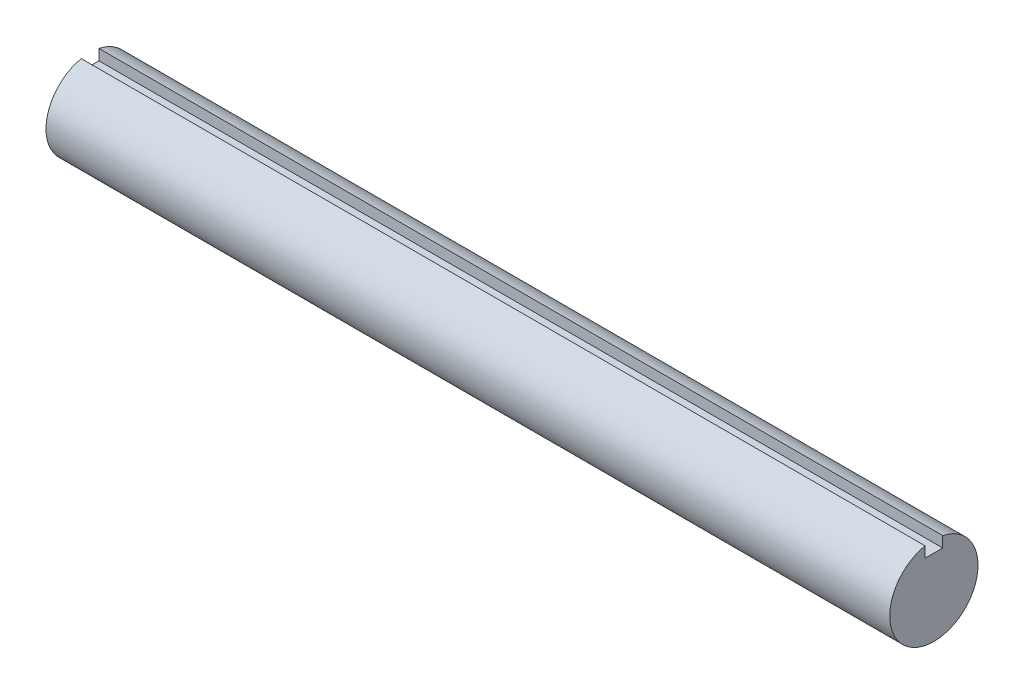
SolidWorks part; units mm, degrees
ref_plane "Front" through (0, 0, 0) normal (0, 0, 1) x (1, 0, 0)
ref_plane "Top" through (0, 0, 0) normal (0, 1, 0) x (1, 0, 0)
ref_plane "Right" through (0, 0, 0) normal (1, 0, 0) x (0, 0, -1)
sketch "AxleProfile" plane through (0, 0, 0) normal (1, 0, 0) x (0, 0, -1)
  line L0 (0, 0) -> (0, 4.8852) construction
  line L1 (-1.331, 6.5042) -> (-1.331, 4.8852)
  line L2 (-1.331, 4.8852) -> (1.331, 4.8852)
  line L3 (1.331, 4.8852) -> (1.331, 6.5042)
  arc A0 (-1.331, 6.5042) -> (1.331, 6.5042) centre (0, 0) ccw
  dimension "D1" = 13.278
  dimension "D2" = 2.662
  dimension "D3" = 1.619
  dimension "D4" = 1.619
extrude "AxleExtrude" add sketch "AxleProfile" along normal blind 127
equation "\"CageLeftBottomEdge\"=22.11mm"
equation "\"CageLeftTopEdge\"=22.11mm"
equation "\"CageRightBottomEdge\"=21.63mm"
equation "\"CageRightTopEdge\"=21.63mm"
equation "\"CageHeight\"=86.04mm"
equation "\"CageLength\"=73.76mm"
equation "\"CageTopScrewClearance\"=10mm"
equation "\"CageBottomScrewClearance\"=25mm"
equation "\"CageLeftTopDepth\"= 11.65mm"
equation "\"CageLeftBottomDepth\"=11.11mm"
equation "\"CageLeftTopHeight\"=8.56175mm"
equation "\"CageLeftBottomHeight\"=16mm"
equation "\"CageRightTopDepth\"= 11.05mm"
equation "\"CageRightBottomDepth\"=10.58mm"
equation "\"CageRightTopHeight\"=9.6mm"
equation "\"CageRightBottomHeight\"=15.49mm"
equation "\"CageLeftTopChannelDepth\"=2.41908mm"
equation "\"CageLeftBottomChannelDepth\"=2.588mm"
equation "\"CageLeftChannelHeight\"=11.7mm"
equation "\"CageRightTopChannelDepth\"=2.32mm"
equation "\"CageRightBottomChannelDepth\"=2.318mm"
equation "\"CageRightChannelHeight\"=10mm"
equation "\"CageChanRelHeight\"=23.99mm"
equation "\"CageChanRelDepth\"=5.492mm"
equation "\"CageChamberRadius\"=16.261mm"
equation "\"CageScrewDiameter\"=4.8mm"
equation "\"CageSetScrewDiameter\"=3.5mm"
equation "\"CageAxleRadius\"=6.639mm"
equation "\"CageAxleKeyHeight\"=1.619mm"
equation "\"CageAxleKeyWidth\"=2.662mm"
equation "\"CageHoseWindowWidth\"=16.29mm"
equation "\"CageHoseWindowHeight\"=26.5mm"
equation "\"CageHoseWindow-Edge\"=8.89mm"
equation "\"CageScrew-VerticalEdge\"=5.0mm"
equation "\"CageScrew-HorizontalEdge\"=7.5mm"
equation "\"CageScrew-HoseCornerScrewEdge\"=4.45mm"
equation "\"CageAxle-BottomEdge\"=56.05mm"
equation "\"CageAxle-FrontEdge\"=46.03mm"
equation "\"CageBackSetScrew-Axle\"=40mm"
equation "\"CageFrontSetScrew-Axle\"=22mm"
equation "\"CageVelocityWindow-BackEdge\"=34.8mm"
equation "\"CageVelocityWindow-BottomEdge\"=27.55mm"
equation "\"CageVelocityWindowHeight\"=22.29mm"
equation "\"CageVelocityWindowWidth\"=12.61mm"
equation "\"TriggerSlot-BottomEdge\"=6.35mm"
equation "\"TriggerSlot-FrontEdge\"=15mm"
equation "\"TriggerSlotSize\"=6.7mm"
equation "\"TriggerRackOffset\"=6mm"
equation "\"TriggerSlotSizeInt\"=.25in"
equation "\"MotorMountLegLength\"=.25in"
equation "\"GearOffset\"=.264907in"
equation "\"TriggerSlotSpacing\"=.25in"
equation "\"TriggerMiniSlotWidth\"=3.5mm"
equation "\"TriggerRackWidth\"=6.5mm"
equation "\"gearhubintdiam\"=30mm"
equation "\"gearhubintwid\"=12.21mm"
equation "\"vigorwidth\"= 0.472441in"
equation "\"vigorflangewidth\"= 0.731102in"
equation "\"vigorflangelength\"= 0.131102in"
equation "\"vigorscrewsize\"= 0.066535in"
equation "\"vigorholeoffsetwid\"= 0.0646653in"
equation "\"vigorholeoffsetlen\"= 0.065551in"
equation "\"vigorflangedepth\"= 0.0901575in"
equation "\"vigordiscdepth\"= 0.0492126in"
equation "\"vigormotordepth\"= 1.12362in"
equation "\"vigortipdepth\"= 0.259055in"
equation "\"vigoraxlewidth\"= 0.173622in"
equation "\"vigorcutlen\"= 0.0480315in"
equation "\"vigoraxledepth\"= 0.159055in"
equation "\"pandiscradius\"=14in"
equation "\"towermaterialwidth\"=.25in"
equation "\"towerslotlength\"=.5in"
equation "\"towermarkerspace\"=5in"
equation "\"towerslothorizoffset\"=1in"
equation "\"towerslothorizspacing\"=2in"
equation "\"towerslotvertoffset\"=3in"
equation "\"towerslotvertspacing\"=1in"
equation "\"towerheight\"=12in"
equation "\"towerupslot\"=1in"
equation "\"toweraxle\"=.5in"
equation "\"towerspeedwidth\"=2in"
equation "\"towerspeedheight\"=8in"
equation "\"towerspeedgap\"=2in"
equation "\"stepperouterrad\"=10mm"
equation "\"stepperscrewsize\"=3.45mm"
equation "\"stepperscrewc2c\"=49.5mm"
equation "\"stepperdepthoffset\"=24mm"
equation "\"stepperhorizoffset\"=22.91mm"
equation "\"stepperaxleflat\"=.037in"
equation "\"stepperaxlerad\"=0.11811024in"
equation "\"shaftslotOD\"=18.8mm"
equation "\"shaftslotID\"=13.28mm"
equation "\"shaftkeywidth\"=2.67mm"
equation "\"shaftkeydepth\"=1.8mm"
equation "\"shaftcollartotaldepth\"=9.71mm"
equation "\"shaftsquaredepth\"=6mm"
equation "\"shaftsetscrewsize\"=3.5mm"
equation "\"shaftkeytightdepth\"=1.85mm"
equation "\"shaftslottightID\"=12.78mm"
equation "\"shaftsetscrewoffset\"=9mm"
equation "\"cagecollartotaldepth\"=20mm"
equation "\"cagecollartotalwidth\"=35mm"
equation "\"cagecollarbasedepth\"=4mm"
equation "\"ajaxaxlesize\"=3.87mm"
equation "\"ajaxinnercut\"=2.3mm"
equation "\"ajaxwidth\"=6.1mm"
equation "\"ajaxdiametral\"=25.8854"
equation "\"ajaxcutoutdepth\"=2.3mm"
equation "\"ajax4020gap\"=29.5mm"
equation "\"ajax4010gap\"=24.5mm"
equation "\"ajax20hubbuffer\"=6.1mm"
equation "\"ajax20hubholeoffset\"=.19685in"
equation "\"ajax20hubholesize\"=.059055in"
equation "\"ajax20cutoutint\"=13.4mm"
equation "\"ajax40hubholesize\"=7.21mm"
equation "\"ajax40hubholeoffset\"=10mm"
equation "\"ajax40hubbuffer\"=8.9mm"
equation "\"ajax40cutoutint\"=32.6mm"
equation "\"bearingpandiscrad\"=6.8in"
equation "\"bearingpandiscang\"=48.75deg"
equation "\"bearingclearholedist\"=4.7345in"
equation "\"bearingclearholesize\"=.5in"
equation "\"bearingclearholeang\"=22.5deg"
equation "\"bearingmountholedist\"=4.25in"
equation "\"bearingwirehole\"=1.5in"
equation "\"no6diam\"=.146in"
equation "\"shortconangle\"=20deg"
equation "\"shortconlen\"=.875in"
equation "\"longconlen\"=1.25in"
equation "\"longconangle\"=15deg"
equation "\"BrassInsertDiameter\"=5.04mm"
equation "\"D1@AxleProfile\"=\"CageAxleRadius\"*2"
equation "\"D2@AxleProfile\"=\"CageAxleKeyWidth\""
equation "\"D3@AxleProfile\"=\"CageAxleKeyHeight\""
equation "\"D4@AxleProfile\"=\"CageAxleKeyHeight\""
equation "\"AxleLength\" = 5.00in"
equation "\"D1@AxleExtrude\"=\"AxleLength\""
